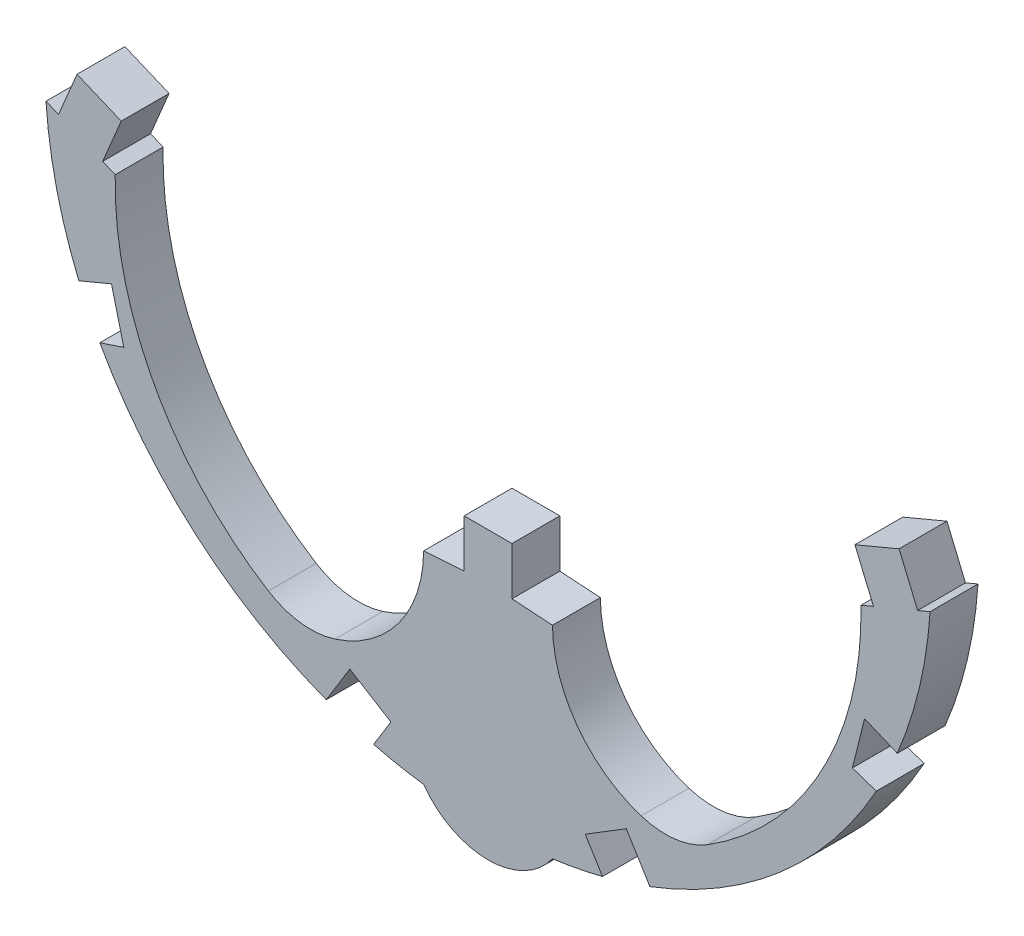
SolidWorks part; units mm, degrees
ref_plane "Front Plane" through (0, 0, 0) normal (0, 0, 1) x (1, 0, 0)
ref_plane "Top Plane" through (0, 0, 0) normal (0, 1, 0) x (1, 0, 0)
ref_plane "Right Plane" through (0, 0, 0) normal (1, 0, 0) x (0, 0, -1)
sketch "Sketch1" plane through (0, 0, 0) normal (0, 0, 1) x (1, 0, 0)
  line L0 (107.5622, 0) -> (106.8002, 0)
  line L1 (106.8002, 0) -> (108.3242, 0) construction
  line L2 (106.8002, 0) -> (106.8002, -1.524)
  line L3 (106.8002, -1.524) -> (105.5122, -1.6085)
  line L4 (93.491, 4.7761) -> (93.8897, 4.6087)
  line L5 (95.2949, 4.0189) -> (95.6936, 3.8516)
  line L6 (95.2949, 4.0189) -> (95.8848, 5.4241)
  line L7 (93.8897, 4.6087) -> (94.4795, 6.014)
  line L8 (107.5622, 0) -> (107.5622, 15.6788) construction
  line L9 (95.8848, 5.4241) -> (94.4795, 6.014)
  line L10 (119.2396, 5.4241) -> (120.6448, 6.014)
  line L11 (121.2346, 4.6087) -> (120.6448, 6.014)
  line L12 (119.8294, 4.0189) -> (119.2396, 5.4241)
  line L13 (119.8294, 4.0189) -> (119.4307, 3.8516)
  line L14 (121.6333, 4.7761) -> (121.2346, 4.6087)
  line L15 (108.3242, -1.524) -> (109.6121, -1.6085)
  line L16 (107.5622, 0) -> (108.3242, 0)
  line L17 (108.3242, 0) -> (108.3242, -1.524)
  line L18 (108.3242, -1.524) -> (108.3203, -1.5299)
  line L19 (120.5874, 0.3476) -> (119.5485, 0.7827)
  line L20 (119.9206, -1.0268) -> (119.1574, -0.7708)
  line L21 (119.1574, -0.7708) -> (119.5485, 0.7827)
  line L22 (94.5369, 0.3476) -> (95.5758, 0.7827)
  line L23 (111.2046, -7.7405) -> (110.6553, -6.8476)
  line L24 (110.6553, -6.8476) -> (111.9626, -6.0435)
  line L25 (111.9626, -6.0435) -> (112.7135, -7.2643)
  line L26 (95.9669, -0.7708) -> (95.5758, 0.7827)
  line L27 (95.2037, -1.0268) -> (95.9669, -0.7708)
  line L28 (103.1617, -6.0435) -> (102.4108, -7.2643)
  line L29 (104.469, -6.8476) -> (103.1617, -6.0435)
  line L30 (103.9197, -7.7405) -> (104.469, -6.8476)
  arc A0 (105.5122, -1.6085) -> (102.6917, -5.4515) centre (101.4504, -1.5839) cw
  arc A1 (100.5693, -5.187) -> (95.6936, 3.8516) centre (106.0702, 3.6148) cw
  arc A2 (93.491, 4.7761) -> (94.5369, 0.3476) centre (107.3349, 5.7078) ccw
  arc A3 (121.6333, 4.7761) -> (120.5874, 0.3476) centre (107.7894, 5.7078) cw
  arc A4 (114.555, -5.187) -> (119.4307, 3.8516) centre (109.0541, 3.6148) ccw
  arc A5 (109.6121, -1.6085) -> (112.4326, -5.4515) centre (113.6739, -1.5839) ccw
  arc A6 (109.6121, -8.0472) -> (105.5122, -8.0472) centre (107.5622, -6.5848) cw
  arc A7 (119.9206, -1.0268) -> (112.7135, -7.2643) centre (107.7894, 5.7078) cw
  arc A8 (111.2046, -7.7405) -> (109.6121, -8.0472) centre (107.7894, 5.7078) cw
  arc A9 (114.555, -5.187) -> (112.4326, -5.4515) centre (113.2088, -3.033) cw
  arc A10 (102.6917, -5.4515) -> (100.5693, -5.187) centre (101.9155, -3.033) cw
  arc A11 (103.9197, -7.7405) -> (105.5122, -8.0472) centre (107.3349, 5.7078) ccw
  arc A12 (95.2037, -1.0268) -> (102.4108, -7.2643) centre (107.3349, 5.7078) ccw
  point P47 (113.7426, -5.6452)
  point P50 (101.3817, -5.6452)
  dimension "D1" = 2.54
  dimension "D2" = 2.54
extrude "Boss-Extrude1" add sketch "Sketch1" along normal blind 1.524
